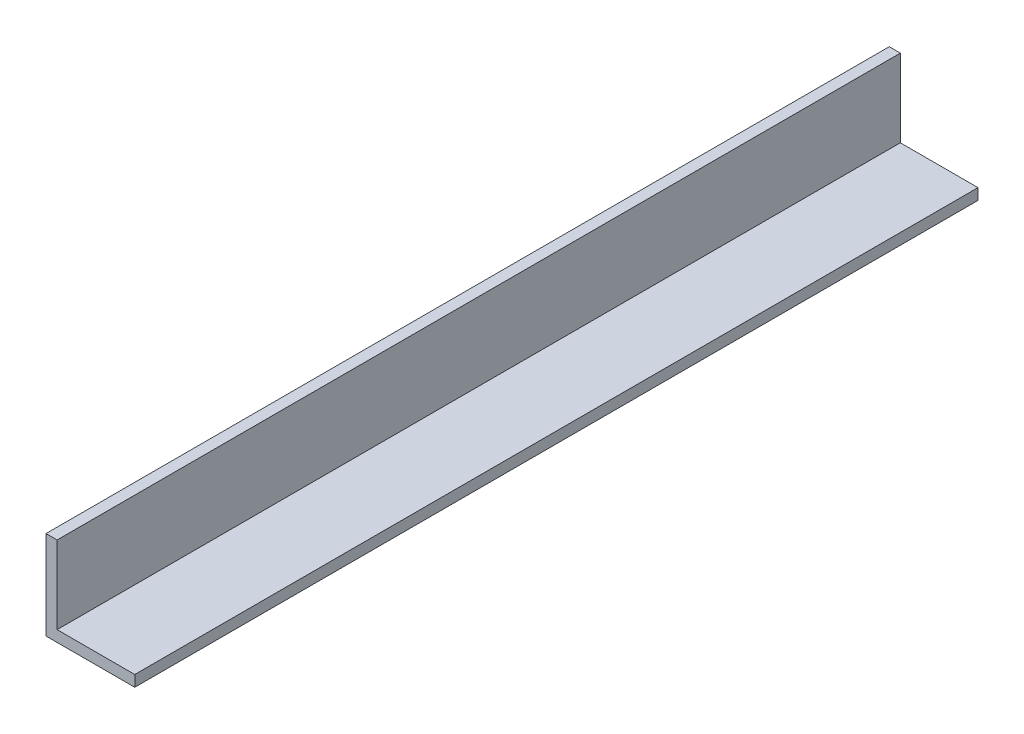
SolidWorks part; units mm, degrees
ref_plane "Front Plane" through (0, 0, 0) normal (0, 0, 1) x (1, 0, 0)
ref_plane "Top Plane" through (0, 0, 0) normal (0, 1, 0) x (1, 0, 0)
ref_plane "Right Plane" through (0, 0, 0) normal (1, 0, 0) x (0, 0, -1)
sketch "Sketch1" plane through (0, 0, 0) normal (0, 0, 1) x (1, 0, 0)
  line L1 (0, 0) -> (25.4, 0)
  line L2 (0, 0) -> (0, 3.175)
  line L3 (0, 3.175) -> (25.4, 3.175)
  line L4 (25.4, 0) -> (25.4, 3.175)
  line L5 (0, 3.175) -> (3.175, 3.175)
  line L6 (0, 3.175) -> (0, 25.4)
  line L7 (0, 25.4) -> (3.175, 25.4)
  line L8 (3.175, 3.175) -> (3.175, 25.4)
  dimension "D1" = 3.175
  dimension "D2" = 25.4
  dimension "D3" = 22.225
  dimension "D4" = 3.175
extrude "Boss-Extrude1" add sketch "Sketch1" along normal blind 241.3 contours L3 L8 L7 L6 | L1 L4 L3 L2
